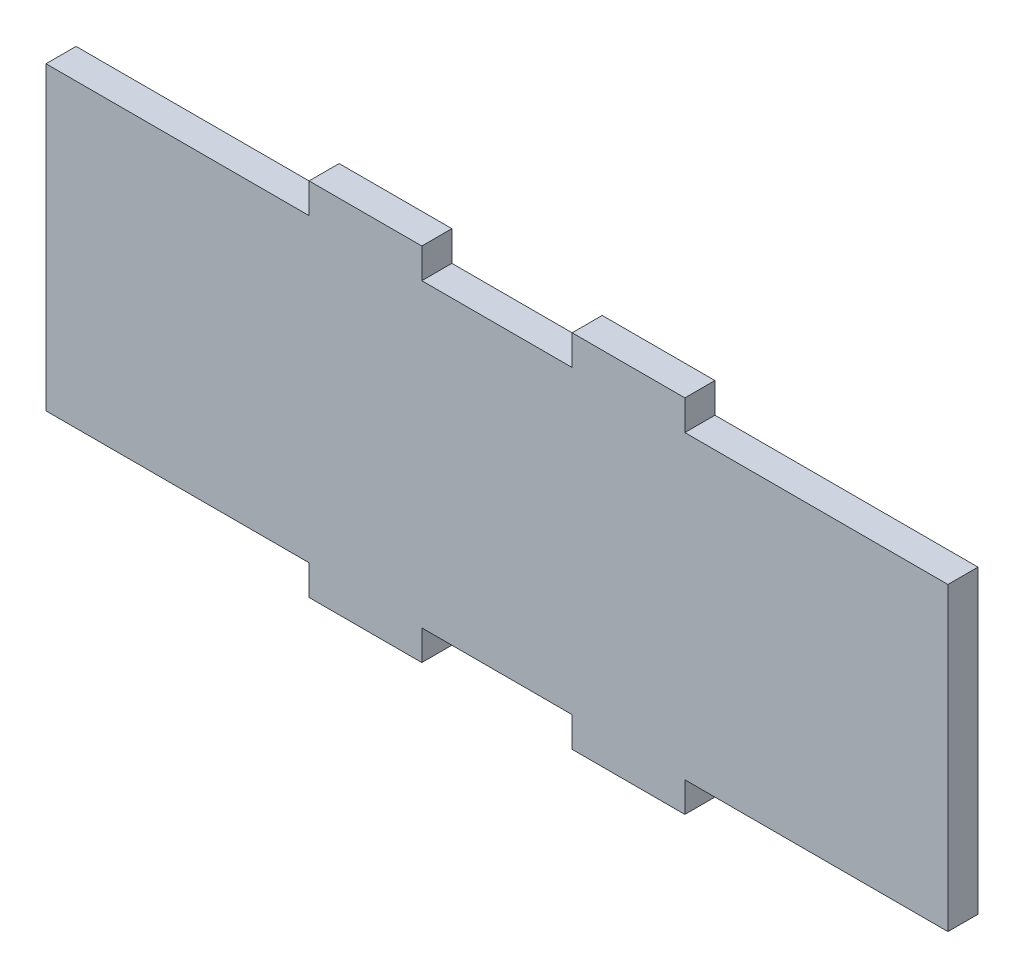
SolidWorks part; units mm, degrees
ref_plane "Front Plane" through (0, 0, 0) normal (0, 0, 1) x (1, 0, 0)
ref_plane "Top Plane" through (0, 0, 0) normal (0, 1, 0) x (1, 0, 0)
ref_plane "Right Plane" through (0, 0, 0) normal (1, 0, 0) x (0, 0, -1)
sketch "Sketch1" plane through (0, 0, 0) normal (0, 1, 0) x (1, 0, 0)
  line L1 (-60, 2) -> (60, 2)
  line L2 (-60, 2) -> (-60, -2)
  line L3 (-60, -2) -> (60, -2)
  line L4 (60, 2) -> (60, -2)
  line L5 (-60, 2) -> (60, -2) construction
  line L6 (-60, -2) -> (60, 2) construction
  point P0 (0, 0)
  dimension "D1" = 4
  dimension "D2" = 120
extrude "Boss-Extrude3" add sketch "Sketch1" along normal blind 48
sketch "Sketch4" plane through (0, 0, 2) normal (0, 0, 1) x (1, 0, 0)
  line L0 (-60, 48) -> (60, 48) construction
  line L1 (-25, 48) -> (-10, 48)
  line L2 (-25, 48) -> (-25, 44)
  line L3 (-25, 44) -> (-10, 44)
  line L4 (-10, 48) -> (-10, 44)
  line L5 (2.2, 0) -> (-2.2, 0) construction
  line L6 (10, 48) -> (25, 48)
  line L7 (10, 48) -> (10, 44)
  line L8 (10, 44) -> (25, 44)
  line L9 (25, 48) -> (25, 44)
  line L10 (-25, 4) -> (-10, 4)
  line L11 (-25, 4) -> (-25, 0)
  line L12 (-25, 0) -> (-10, 0)
  line L13 (-10, 4) -> (-10, 0)
  line L14 (0, -2.2) -> (0, 2.2) construction
  line L15 (10, 4) -> (25, 4)
  line L16 (10, 4) -> (10, 0)
  line L17 (10, 0) -> (25, 0)
  line L18 (25, 4) -> (25, 0)
  line L19 (-60, 48) -> (-60, 0) construction
  line L20 (60, 48) -> (60, 0) construction
  line L21 (-60, 48) -> (-60, 0)
  line L22 (-60, 48) -> (60, 48)
  line L23 (60, 48) -> (60, 0)
  line L25 (-60, 44) -> (60, 44)
  line L26 (-60, 44) -> (-60, 4)
  line L27 (-60, 4) -> (60, 4)
  line L28 (60, 44) -> (60, 4)
  line M20 (-60, 0) -> (60, 0)
  line M21 (60, 0) -> (60, 48)
  line M22 (60, 48) -> (-60, 48)
  line M23 (-60, 48) -> (-60, 0)
  dimension "D1" = 15
  dimension "D2" = 15
  dimension "D3" = 4
  dimension "D4" = 10
  dimension "D5" = 10
  dimension "D6" = 4
extrude "Cut-Extrude2" cut sketch "Sketch4" against normal blind 48 contours L25 L2 M23 M22 | L4 L25 L7 M22 | L9 L25 L23 M22 | L27 L11 M23 M20 | L27 L13 L16 M20 | L27 L18 M20 M21
